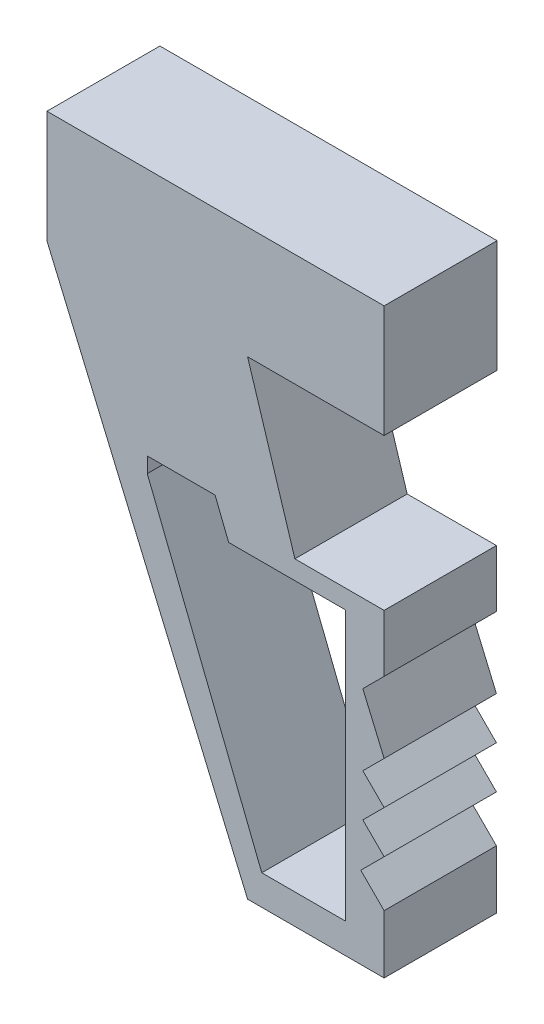
SolidWorks part; units mm, degrees
ref_plane "Front Plane" through (0, 0, 0) normal (0, 0, 1) x (1, 0, 0)
ref_plane "Top Plane" through (0, 0, 0) normal (0, 1, 0) x (1, 0, 0)
ref_plane "Right Plane" through (0, 0, 0) normal (1, 0, 0) x (0, 0, -1)
sketch "Sketch6" plane through (0, 0, 0) normal (0, 1, 0) x (1, 0, 0)
  line L1 (1501.0556, 251.3904) -> (-1501.0556, 251.3904)
  line L2 (1501.0556, 251.3904) -> (1501.0556, -251.3904)
  line L3 (1501.0556, -251.3904) -> (-1501.0556, -251.3904)
  line L4 (-1501.0556, 251.3904) -> (-1501.0556, -251.3904)
  point P0 (0, 0)
extrude "Boss-Extrude4" add sketch "Sketch6" against normal blind 500
sketch "Sketch7" plane through (0, 0, 251.3904) normal (0, 0, 1) x (1, 0, 0)
  line L0 (-1501.0556, -500) -> (-607.8421, -2591.4112)
  line L1 (-607.8421, -2591.4112) -> (0, -2591.4112)
  line L2 (0, -2591.4112) -> (0, -2331.81)
  line L3 (0, -2331.81) -> (-103.9503, -2227.8597)
  line L4 (-103.9503, -2227.8597) -> (0, -2123.9093)
  line L5 (0, -2123.9093) -> (-94.7297, -2029.1797)
  line L6 (-94.7297, -2029.1797) -> (0, -1934.45)
  line L7 (0, -1934.45) -> (-94.7297, -1839.7204)
  line L8 (-94.7297, -1839.7204) -> (0, -1744.9907)
  line L9 (0, -1744.9907) -> (-94.7297, -1523.1863)
  line L10 (-94.7297, -1523.1863) -> (0, -1428.4567)
  line L11 (0, -1428.4567) -> (0, -1173.9747)
  line L12 (0, -1173.9747) -> (-397.3317, -1173.9747)
  line L13 (-397.3317, -1173.9747) -> (-607.8421, -500)
  line L14 (-1501.0556, -500) -> (1501.0556, -500) construction
  line L15 (-607.8421, -500) -> (-1501.0556, -500)
  line L16 (-1054.4488, -1173.9747) -> (-544.689, -2458.0879)
  line L17 (-172.7873, -2458.0879) -> (-544.689, -2458.0879)
  line L18 (-172.7873, -2458.0879) -> (-172.7873, -1258.1789)
  line L19 (-172.7873, -1258.1789) -> (-692.0462, -1258.1789)
  line L20 (-692.0462, -1258.1789) -> (-752.5918, -1105.6612)
  line L21 (-752.5918, -1105.6612) -> (-1054.4488, -1105.6612)
  line L22 (-1054.4488, -1105.6612) -> (-1054.4488, -1173.9747)
extrude "Boss-Extrude5" add sketch "Sketch7" against normal blind 500
sketch "Sketch8" plane through (0, 0, 251.3904) normal (0, 0, 1) x (1, 0, 0)
  line L1 (0, 0) -> (2223.4461, 0)
  line L2 (0, 0) -> (0, -2751.3748)
  line L3 (0, -2751.3748) -> (2223.4461, -2751.3748)
  line L4 (2223.4461, 0) -> (2223.4461, -2751.3748)
extrude "Cut-Extrude1" cut sketch "Sketch8" against normal blind 1463
